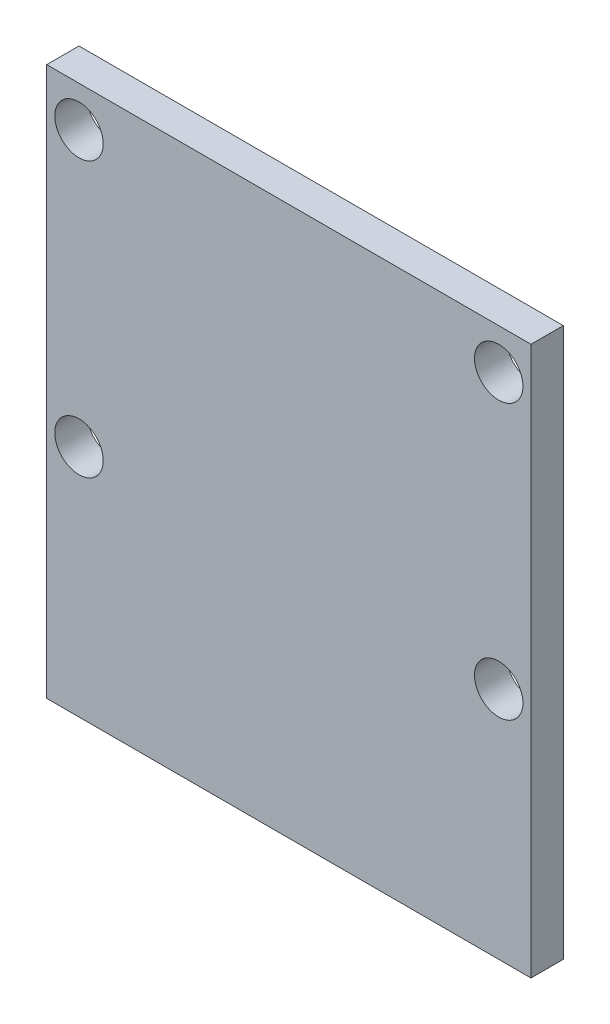
SolidWorks part; units mm, degrees
ref_plane "Front Plane" through (0, 0, 0) normal (0, 0, 1) x (1, 0, 0)
ref_plane "Top Plane" through (0, 0, 0) normal (0, 1, 0) x (1, 0, 0)
ref_plane "Right Plane" through (0, 0, 0) normal (1, 0, 0) x (0, 0, -1)
sketch "Sketch1" plane through (0, 0, 0) normal (0, 0, 1) x (1, 0, 0)
  line L1 (-15, -17) -> (15, -17)
  line L2 (-15, -17) -> (-15, 17)
  line L3 (-15, 17) -> (15, 17)
  line L4 (15, -17) -> (15, 17)
  line L5 (-15, -17) -> (15, 17) construction
  line L6 (-15, 17) -> (15, -17) construction
  circle A0 centre (-13, 14.5) radius 1.5
  circle A1 centre (13, 14.5) radius 1.5
  circle A2 centre (-13, -2.5) radius 1.5
  circle A3 centre (13, -2.5) radius 1.5
  point P0 (0, 0)
  dimension "D5" = 3
  dimension "D6" = 2.5
  dimension "D8" = 3
  dimension "D1" = 30
  dimension "D2" = 34
  dimension "D3" = 2
  dimension "D4" = 2.5
  dimension "D7" = 2
  dimension "D9" = 17
extrude "Boss-Extrude1" add sketch "Sketch1" along normal blind 2
